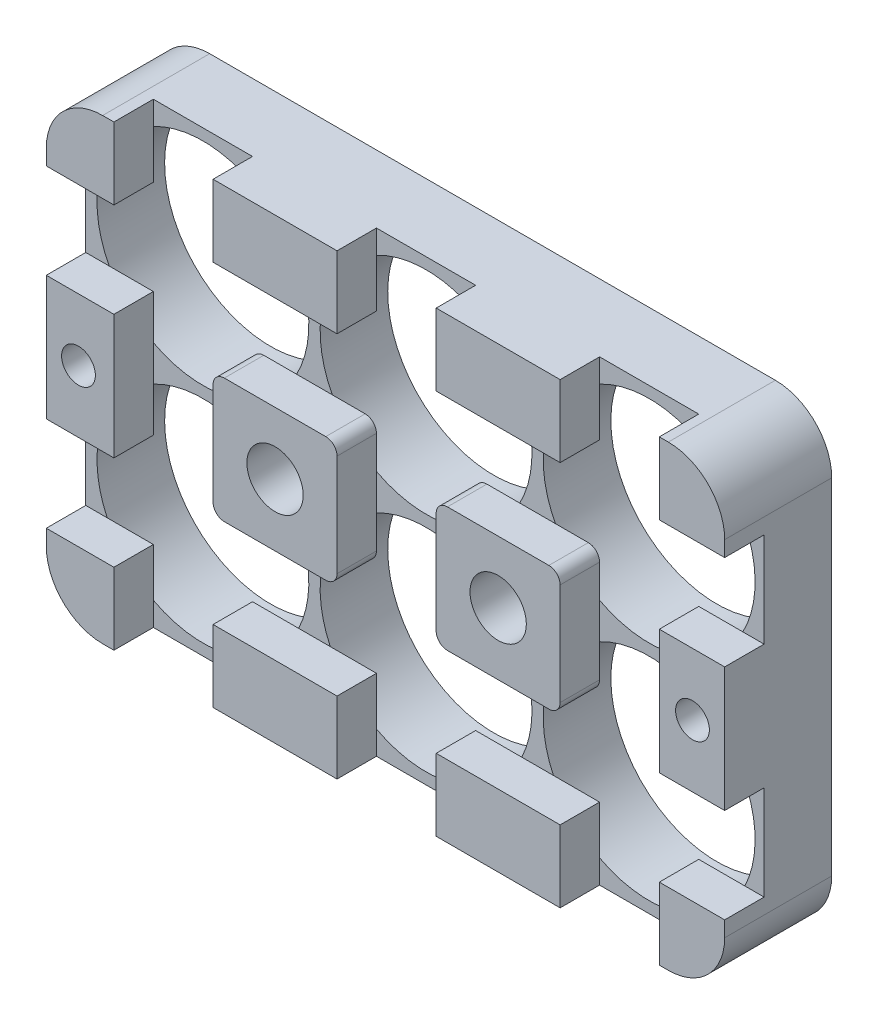
SolidWorks part; units mm, degrees
ref_plane "前视基准面" through (0, 0, 0) normal (0, 0, 1) x (1, 0, 0)
ref_plane "上视基准面" through (0, 0, 0) normal (0, 1, 0) x (1, 0, 0)
ref_plane "右视基准面" through (0, 0, 0) normal (1, 0, 0) x (0, 0, -1)
sketch "草图1" plane through (0, 0, 0) normal (0, 0, 1) x (1, 0, 0)
  line L0 (0, 0) -> (0, 10.4) construction
  line L1 (0, 10.4) -> (-10.4, 10.4) construction
  line L2 (0, -19.8) -> (0, -30.2) construction
  line L3 (0, -30.2) -> (-10.4, -30.2) construction
  line L4 (59.4, 0) -> (59.4, 10.4) construction
  line L5 (59.4, 10.4) -> (49.8, 10.4) construction
  line L6 (39.4, -19.8) -> (49.8, -19.8) construction
  line L7 (49.8, -19.8) -> (49.8, -30.2) construction
  line L8 (-10.4, 10.4) -> (49.8, 10.4)
  line L9 (49.8, 10.4) -> (49.8, -30.2)
  line L10 (49.8, -30.2) -> (-10.4, -30.2)
  line L11 (-10.4, -30.2) -> (-10.4, 10.4)
  line L12 (0, 0) -> (19.8, -19.8) construction
  line L13 (19.8, 0) -> (0, -19.8) construction
  circle A0 centre (0, 0) radius 9.4
  circle A1 centre (19.8, 0) radius 9.4
  circle A2 centre (39.6, 0) radius 9.4
  circle A4 centre (0, -19.8) radius 9.4
  circle A5 centre (19.8, -19.8) radius 9.4
  circle A6 centre (39.6, -19.8) radius 9.4
  circle A8 centre (9.9, -9.9) radius 2.5
  circle A9 centre (29.7, -9.9) radius 2.5
  circle A12 centre (59.4, 0) radius 9.4 [skipped]
  circle A13 centre (49.5, -9.9) radius 2.5 [skipped]
  dimension "D1" = 4
  dimension "D3" = 3
  dimension "D2" = 2
extrude "凸台-拉伸1" add sketch "草图1" along normal blind 6
sketch "草图2" plane through (0, 0, 6) normal (0, 0, 1) x (1, 0, 0)
  line L1 (-10.4, 10.4) -> (49.8, 10.4)
  line L2 (-10.4, 10.4) -> (-10.4, -30.2)
  line L3 (-10.4, -30.2) -> (49.8, -30.2)
  line L4 (49.8, 10.4) -> (49.8, -30.2)
extrude "凸台-拉伸2" add sketch "草图2" along normal blind 3.5
sketch "草图3" plane through (0, 0, 9.5) normal (0, 0, 1) x (1, 0, 0)
  line L0 (-10.4, 10.4) -> (-10.4, 0) construction
  line L1 (-10.4, 10.4) -> (-10.4, -30.2) construction
  line L2 (-10.4, 10.4) -> (-10.4, 4.02) construction
  line L3 (49.8, -30.2) -> (49.8, 10.4) construction
  line L4 (-10.4, 4.02) -> (49.8, 4.02)
  line L5 (-10.4, 4.02) -> (-10.4, -4.38)
  line L6 (-10.4, -4.38) -> (49.8, -4.38)
  line L7 (49.8, 4.02) -> (49.8, -4.38)
  line L8 (-10.4, -9.9) -> (49.8, -9.9) construction
  line L9 (49.8, -9.9) -> (71.0783, -12.0717) construction
  line L10 (-10.4, -15.42) -> (49.8, -15.42)
  line L11 (49.8, -23.82) -> (49.8, -15.42)
  line L12 (-10.4, -23.82) -> (49.8, -23.82)
  line L13 (-10.4, -23.82) -> (-10.4, -15.42)
  line L14 (49.8, -9.9) -> (71.0783, -7.7283) construction
extrude "切除-拉伸1" cut sketch "草图3" against normal blind 3.5
sketch "草图4" plane through (0, 0, 9.5) normal (0, 0, 1) x (1, 0, 0)
  line L0 (-10.4, 10.4) -> (-4.4, 10.4) construction
  line L1 (49.8, 10.4) -> (-10.4, 10.4) construction
  line L2 (-10.4, -30.2) -> (49.8, -30.2) construction
  line L3 (-4.4, 10.4) -> (4.4, 10.4)
  line L4 (-4.4, 10.4) -> (-4.4, -30.2)
  line L5 (-4.4, -30.2) -> (4.4, -30.2)
  line L6 (4.4, 10.4) -> (4.4, -30.2)
  line L7 (15.4, 10.4) -> (15.4, -30.2)
  line L8 (15.4, 10.4) -> (24.2, 10.4)
  line L9 (24.2, 10.4) -> (24.2, -30.2)
  line L10 (15.4, -30.2) -> (24.2, -30.2)
  line L11 (35.2, 10.4) -> (35.2, -30.2)
  line L12 (35.2, 10.4) -> (44, 10.4)
  line L13 (44, 10.4) -> (44, -30.2)
  line L14 (35.2, -30.2) -> (44, -30.2)
  line L15 (55, 10.4) -> (55, -30.2)
  line L16 (55, 10.4) -> (63.8, 10.4)
  line L17 (63.8, 10.4) -> (63.8, -30.2)
  line L18 (55, -30.2) -> (63.8, -30.2)
  dimension "D1" = 4
extrude "切除-拉伸2" cut sketch "草图4" against normal blind 3.5
sketch "草图5" plane through (0, 0, 6) normal (0, 0, -1) x (-1, 0, 0)
  line L1 (-19.7, 10.4) -> (-19.7, -25.8978) construction
  line L2 (-49.8, 10.4) -> (10.4, 10.4) construction
  circle A1 centre (-29.7, -9.9) radius 2.5
  circle A2 centre (-9.9, -9.9) radius 2.5
  circle A3 centre (-46.9443, -9.9) radius 1.5
  circle A4 centre (7.5443, -9.9) radius 1.5
extrude "切除-拉伸3" cut sketch "草图5" against normal blind 10 and the other way blind 10
fillet "圆角3" radius 5 1 edges at (-10.4, -30.2, 4.75)
fillet "圆角8" radius 5 1 edges at (49.8, -30.2, 4.75)
fillet "圆角9" radius 5 1 edges at (49.8, 10.4, 4.75)
fillet "圆角10" radius 5 1 edges at (-10.4, 10.4, 4.75)
fillet "圆角11" radius 1 1 edges at (4.4, -4.38, 7.75)
fillet "圆角12" radius 1 1 edges at (4.4, -15.42, 7.75)
fillet "圆角13" radius 1 1 edges at (15.4, -15.42, 7.75)
fillet "圆角14" radius 1 1 edges at (15.4, -4.38, 7.75)
fillet "圆角15" radius 1 1 edges at (24.2, -15.42, 7.75)
fillet "圆角16" radius 1 1 edges at (35.2, -15.42, 7.75)
fillet "圆角17" radius 1 1 edges at (35.2, -4.38, 7.75)
fillet "圆角18" radius 1 1 edges at (24.2, -4.38, 7.75)
